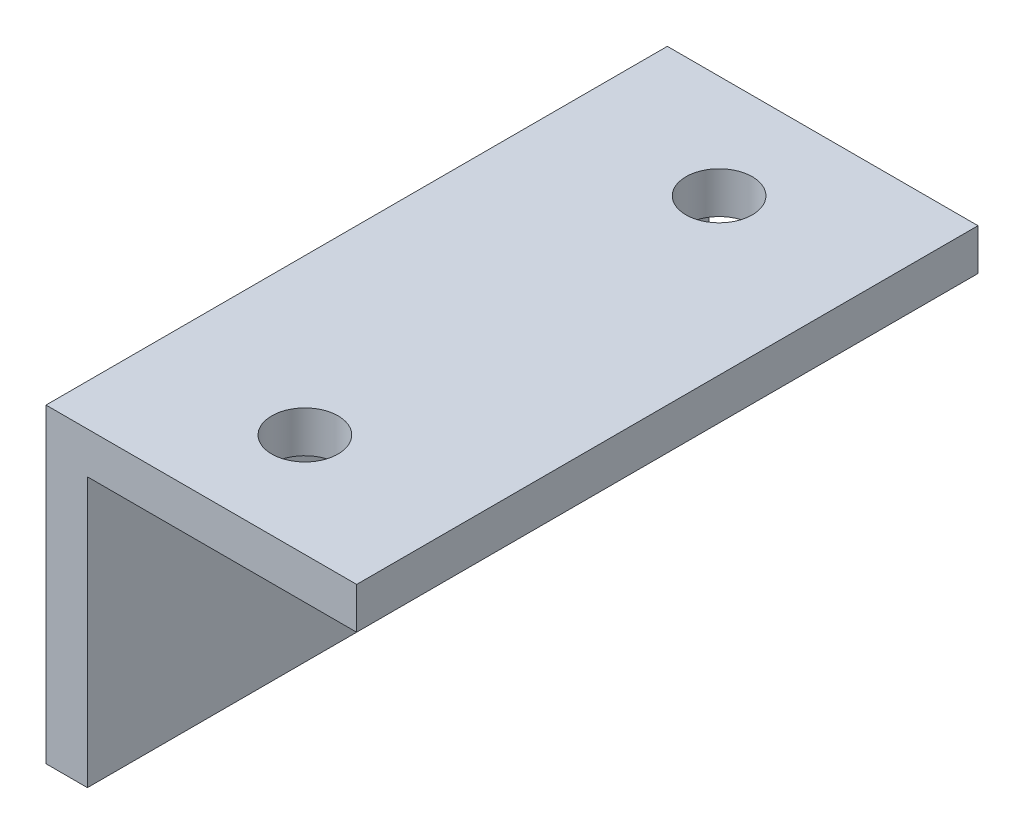
SolidWorks part; units mm, degrees
ref_plane "正面" through (0, 0, 0) normal (0, 0, 1) x (1, 0, 0)
ref_plane "平面" through (0, 0, 0) normal (0, 1, 0) x (1, 0, 0)
ref_plane "右側面" through (0, 0, 0) normal (1, 0, 0) x (0, 0, -1)
sketch "ｽｹｯﾁ1" plane through (0, 0, 0) normal (0, 0, 1) x (1, 0, 0)
  line L0 (0, 0) -> (0, -15)
  line L1 (0, -15) -> (2, -15)
  line L2 (2, -15) -> (2, -2)
  line L3 (2, -2) -> (15, -2)
  line L4 (15, -2) -> (15, 0)
  line L5 (15, 0) -> (0, 0)
  dimension "D1" = 2
  dimension "D2" = 2
  dimension "D3" = 13
  dimension "D4" = 13
  dimension "D5" = 15
  dimension "D6" = 15
extrude "ﾎﾞｽ - 押し出し1" add sketch "ｽｹｯﾁ1" along normal blind 30
sketch "ｽｹｯﾁ2" plane through (0, 0, 0) normal (0, 1, 0) x (1, 0, 0)
  line L0 (7.5, 0) -> (7.5, -5)
  line L1 (15, 0) -> (0, 0) construction
  line L2 (7.5, -5) -> (7.5, -25)
  circle A0 centre (7.5, -5) radius 1.6
  circle A1 centre (7.5, -25) radius 1.6
  dimension "D3" = 3.2
  dimension "D4" = 3.2
  dimension "D1" = 5
  dimension "D2" = 20
extrude "ｶｯﾄ - 押し出し1" cut sketch "ｽｹｯﾁ2" against normal blind 30
sketch "ｽｹｯﾁ3" plane through (0, 0, 0) normal (-1, 0, 0) x (0, 0, 1)
  line L0 (0, -7.5) -> (15, -7.5)
  line L1 (0, 0) -> (0, -15) construction
  line L2 (15, -7.5) -> (15, -9)
  circle A0 centre (15, -9) radius 2.1
  dimension "D3" = 4.2
  dimension "D1" = 15
  dimension "D2" = 1.5
extrude "ｶｯﾄ - 押し出し2" cut sketch "ｽｹｯﾁ3" against normal blind 30
